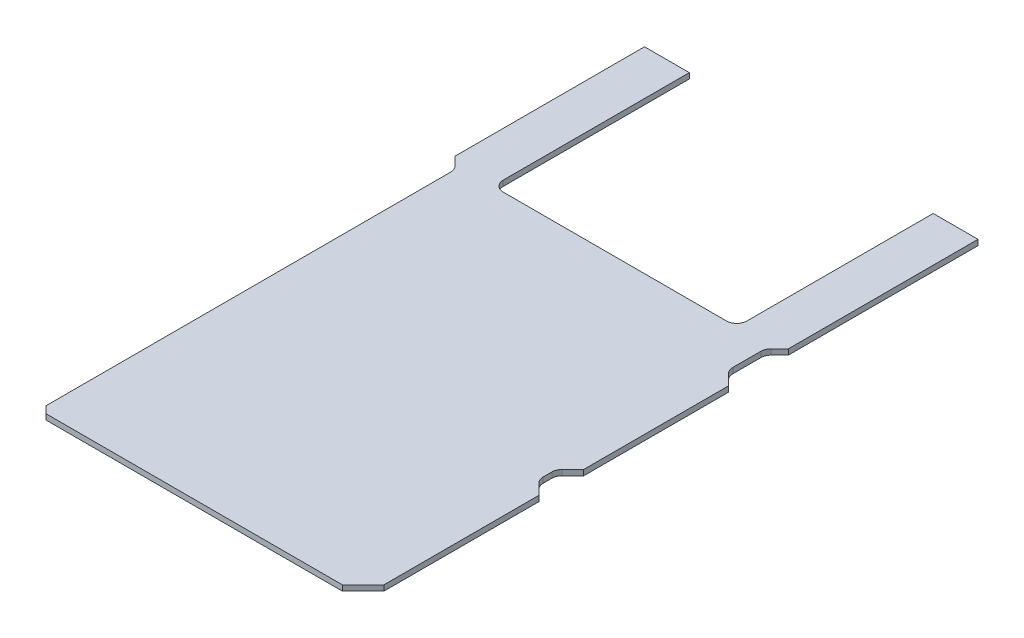
SolidWorks part; units mm, degrees
ref_plane "Front Plane" through (0, 0, 0) normal (0, 0, 1) x (1, 0, 0)
ref_plane "Top Plane" through (0, 0, 0) normal (0, 1, 0) x (1, 0, 0)
ref_plane "Right Plane" through (0, 0, 0) normal (1, 0, 0) x (0, 0, -1)
sketch "Sketch1" plane through (0, 0, 0) normal (0, 1, 0) x (1, 0, 0)
  line L1 (45, -88.5) -> (-45, -88.5)
  line L2 (45, -88.5) -> (45, 88.5)
  line L3 (45, 88.5) -> (-45, 88.5)
  line L4 (-45, -88.5) -> (-45, 88.5)
  line L5 (45, -88.5) -> (-45, 88.5) construction
  line L6 (45, 88.5) -> (-45, -88.5) construction
  point P0 (0, 0)
  dimension "D1" = 90
  dimension "D2" = 177
extrude "Boss-Extrude1" add sketch "Sketch1" along normal blind 1.6
sketch "Sketch5" plane through (0, 0, 0) normal (0, -1, 0) x (1, 0, 0)
  line L0 (45, 88.5) -> (45, -88.5) construction
  line L1 (37.6, -44) -> (37.6, -48)
  line L2 (37.6, -44) -> (22.4, -44)
  line L3 (22.4, -44) -> (22.4, -48)
  line L4 (37.6, -48) -> (22.4, -48)
  line L5 (16.1, -44) -> (16.1, -48)
  line L6 (16.1, -44) -> (0.9, -44)
  line L7 (0.9, -44) -> (0.9, -48)
  line L8 (16.1, -48) -> (0.9, -48)
  line L9 (37.6, -80) -> (37.6, -84)
  line L10 (37.6, -80) -> (22.4, -80)
  line L11 (22.4, -80) -> (22.4, -84)
  line L12 (37.6, -84) -> (22.4, -84)
  line L13 (12.1, -80) -> (12.1, -84)
  line L14 (12.1, -80) -> (-3.1, -80)
  line L15 (-3.1, -80) -> (-3.1, -84)
  line L16 (12.1, -84) -> (-3.1, -84)
  line L17 (2.025, -44.54) -> (14.975, -44.54)
  line L18 (2.025, -44.54) -> (2.025, -47.46)
  line L19 (2.025, -47.46) -> (14.975, -47.46)
  line L20 (14.975, -44.54) -> (14.975, -47.46)
  line L21 (23.525, -44.54) -> (36.475, -44.54)
  line L22 (23.525, -44.54) -> (23.525, -47.46)
  line L23 (23.525, -47.46) -> (36.475, -47.46)
  line L24 (36.475, -44.54) -> (36.475, -47.46)
  line L25 (-1.975, -80.54) -> (10.975, -80.54)
  line L26 (-1.975, -80.54) -> (-1.975, -83.46)
  line L27 (-1.975, -83.46) -> (10.975, -83.46)
  line L28 (10.975, -80.54) -> (10.975, -83.46)
  line L29 (23.525, -80.54) -> (36.475, -80.54)
  line L30 (23.525, -80.54) -> (23.525, -83.46)
  line L31 (23.525, -83.46) -> (36.475, -83.46)
  line L32 (36.475, -80.54) -> (36.475, -83.46)
  line L33 (-22, -41.5) -> (43, -41.5) construction
  line L34 (-22, -41.5) -> (-22, -86.5) construction
  line L35 (-22, -86.5) -> (43, -86.5) construction
  line L36 (43, -41.5) -> (43, -86.5) construction
  line L37 (45, -88.5) -> (-45, -88.5) construction
  point P16 (8.5, -44)
  point P17 (30, -44)
  point P18 (4.5, -84)
  point P19 (30, -84)
  point P25 (37.6, -82)
  point P26 (37.6, -46)
  point P38 (8.5, -44.54)
  point P39 (2.025, -46)
  point P40 (0.9, -46)
  point P41 (30, -44.54)
  point P42 (-1.975, -82)
  point P43 (-3.1, -82)
  point P44 (4.5, -83.46)
  point P45 (30, -83.46)
  dimension "D1" = 15.2
  dimension "D2" = 4
  dimension "D3" = 21.5
  dimension "D4" = 25.5
  dimension "D5" = 2.92
  dimension "D6" = 12.95
  dimension "D7" = 36
  dimension "D8" = 65
  dimension "D9" = 45
  dimension "D10" = 2.5
  dimension "D11" = 5.4
  dimension "D12" = 2
  dimension "D13" = 2
sketch "Sketch7" plane through (0, 0, 0) normal (0, -1, 0) x (1, 0, 0)
  line L0 (-45, -30.1257) -> (-48.3743, -33.5)
  line L1 (-45, -88.5) -> (-48.3743, -88.5)
  line L2 (-45, -88.5) -> (-45, -30.1257)
  line L4 (-48.3743, -88.5) -> (-48.3743, -33.5)
  line L5 (45, -88.5) -> (48.3743, -88.5)
  line L6 (45, -88.5) -> (45, -30.1257)
  line L8 (48.3743, -88.5) -> (48.3743, -33.5)
  line L9 (45, -30.1257) -> (48.3743, -33.5)
  line M9 (-45, 88.5) -> (-45, -88.5)
  line M11 (45, -88.5) -> (45, 88.5)
  dimension "D1" = 3.3743
  dimension "D2" = 55
  dimension "D3" = 45
extrude "Boss-Extrude4" add sketch "Sketch7" against normal up to surface (1.6 mm away) contours L4 L1 L0 M9 | L9 L5 L8 M11 up to face at (0, 1.6, 0)
sketch "w" plane through (0, 1.6, 0) normal (0, 1, 0) x (1, 0, 0)
  line L0 (45, -88.5) -> (49, -84.5)
  line L1 (45, -88.5) -> (45, 30.1257) construction
  line L2 (49, -84.5) -> (49, -39.5)
  line L3 (49, -39.5) -> (45, -35.5)
  line L4 (45, -30.5) -> (49, -26.5)
  line L5 (49, -26.5) -> (49, 15.5)
  line L6 (49, 15.5) -> (45, 19.5)
  line L7 (45, 19.5) -> (45, -30.5)
  line L8 (45, -35.5) -> (45, -88.5)
  line L9 (-45, -88.5) -> (45, -88.5) construction
  line L10 (-45, -88.5) -> (-43, -90.5)
  line L11 (-43, -90.5) -> (43, -90.5)
  line L12 (43, -90.5) -> (45, -88.5)
  line L13 (-45, -88.5) -> (45, -88.5)
  line M54 (-45, -88.5) -> (45, -88.5)
  line M55 (45, -88.5) -> (45, 30.1257)
  dimension "D1" = 4
  dimension "D2" = 45
  dimension "D3" = 53
  dimension "D4" = 50
  dimension "D5" = 5
  dimension "D6" = 2
extrude "Boss-Extrude5" add sketch "w" against normal up to surface (1.6 mm away) contours L11 L12 L10 M54 | L2 L3 L0 M55 | L5 L6 L4 M55 up to face at (0, 0, -15.9064)
sketch "Sketch9" plane through (0, 0, 0) normal (0, -1, 0) x (1, 0, 0)
  line L0 (48.3743, -88.5) -> (-48.3743, -88.5) construction
  line L1 (-35.3743, -88.5) -> (35.3743, -88.5)
  line L2 (-35.3743, -88.5) -> (-35.3743, -31.5)
  line L3 (-35.3743, -31.5) -> (35.3743, -31.5)
  line L4 (35.3743, -88.5) -> (35.3743, -31.5)
  line L5 (48.3743, -88.5) -> (48.3743, -33.5) construction
  line L6 (-48.3743, -88.5) -> (-48.3743, -33.5) construction
  dimension "D1" = 13
  dimension "D2" = 13
  dimension "D3" = 57
extrude "Cut-Extrude3" cut sketch "Sketch9" against normal through all
fillet "Fillet1" radius 3 7 edges at (45, 0.8, -30.1257) (-45, 0.8, -30.1257) (45, 0.8, -19.5) (45, 0.8, 30.5) (45, 0.8, 35.5) (-35.3743, 0.8, -31.5) (35.3743, 0.8, -31.5)
